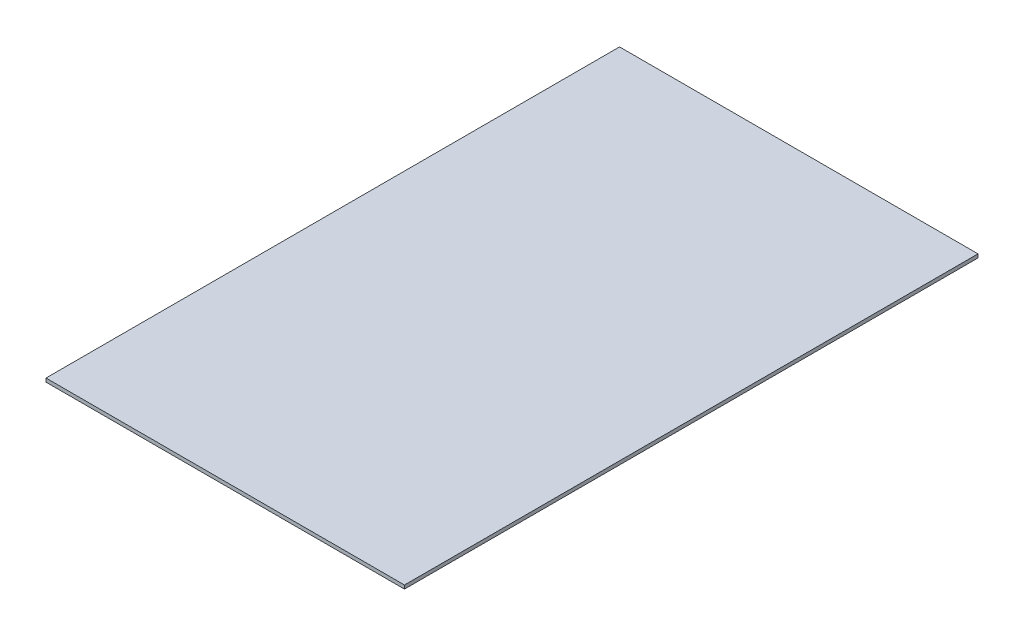
SolidWorks part; units mm, degrees
ref_plane "前视基准面" through (0, 0, 0) normal (0, 0, 1) x (1, 0, 0)
ref_plane "上视基准面" through (0, 0, 0) normal (0, 1, 0) x (1, 0, 0)
ref_plane "右视基准面" through (0, 0, 0) normal (1, 0, 0) x (0, 0, -1)
sketch "草图1" plane through (0, 0, 0) normal (0, 1, 0) x (1, 0, 0)
  line L1 (-2358.1081, 1542.5676) -> (-1358.1081, 1542.5676)
  line L2 (-2358.1081, 1542.5676) -> (-2358.1081, -57.4324)
  line L3 (-2358.1081, -57.4324) -> (-1358.1081, -57.4324)
  line L4 (-1358.1081, 1542.5676) -> (-1358.1081, -57.4324)
  line L5 (-2358.1081, 1542.5676) -> (-1358.1081, -57.4324) construction
  line L6 (-2358.1081, -57.4324) -> (-1358.1081, 1542.5676) construction
  point P0 (-1858.1081, 742.5676)
  dimension "D1" = 1000
  dimension "D2" = 1600
extrude "凸台-拉伸1" add sketch "草图1" along normal blind 10
